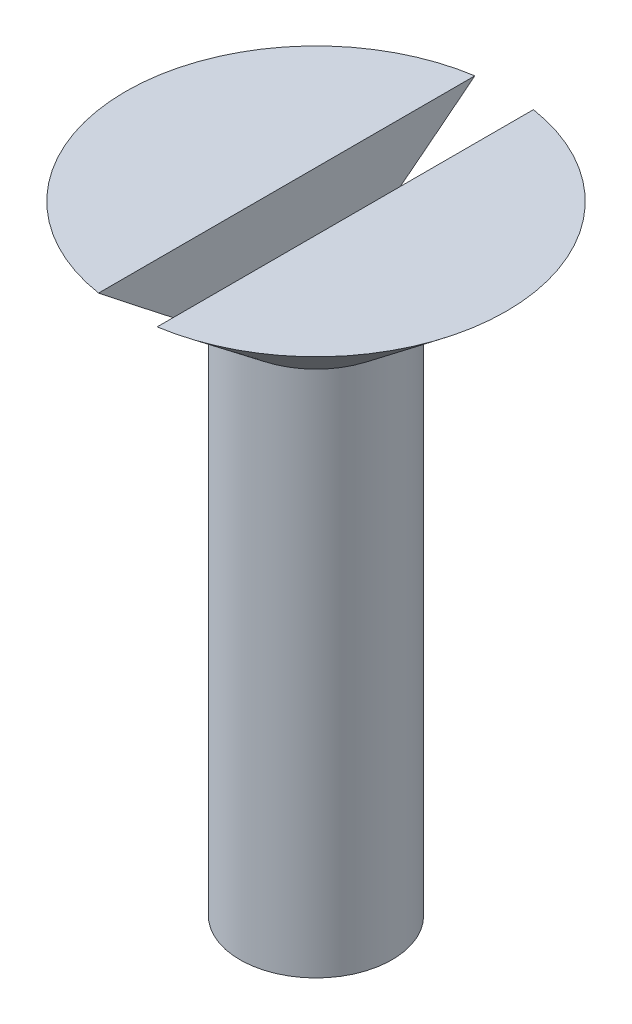
SolidWorks part; units mm, degrees
ref_plane "Front Plane" through (0, 0, 0) normal (0, 0, 1) x (1, 0, 0)
ref_plane "Top Plane" through (0, 0, 0) normal (0, 1, 0) x (1, 0, 0)
ref_plane "Right Plane" through (0, 0, 0) normal (1, 0, 0) x (0, 0, -1)
sketch "Sketch1" plane through (0, 0, 0) normal (0, 0, 1) x (1, 0, 0)
  line L0 (0, 0) -> (2.5981, 1.5)
  line L1 (2.5981, 1.5) -> (2.5981, 19.5)
  line L2 (2.5981, 19.5) -> (6.5, 22.6265)
  line L3 (6.5, 22.6265) -> (0, 22.6265)
  line L4 (0, 22.6265) -> (0, 0)
  dimension "D1" = 18
  dimension "D2" = 3
  dimension "D3" = 60
  dimension "D4" = 6.5
  dimension "D5" = 5
revolve "Revolve1" add sketch "Sketch1" angle 360 about L4
sketch "Sketch3" plane through (0, 22.6265, 0) normal (0, 1, 0) x (1, 0, 0)
  line L1 (-1, -7.5) -> (1, -7.5)
  line L2 (-1, -7.5) -> (-1, 7.5)
  line L3 (-1, 7.5) -> (1, 7.5)
  line L4 (1, -7.5) -> (1, 7.5)
  line L5 (-1, -7.5) -> (1, 7.5) construction
  line L6 (-1, 7.5) -> (1, -7.5) construction
  point P0 (0, 0)
  dimension "D1" = 2
  dimension "D2" = 15
extrude "Cut-Extrude1" cut sketch "Sketch3" against normal blind 2
